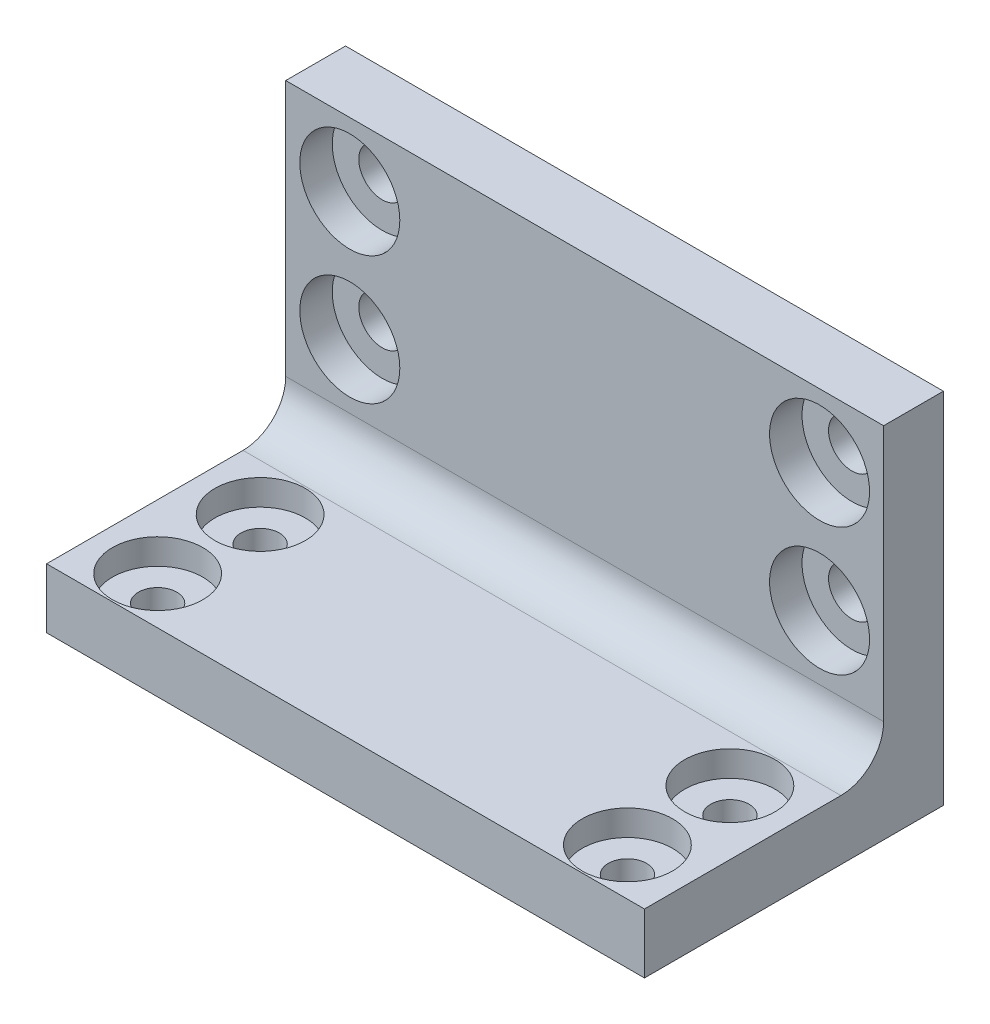
SolidWorks part; units mm, degrees
material "201 Annealed Stainless Steel (SS)"
ref_plane "Front Plane" through (0, 0, 0) normal (0, 0, 1) x (1, 0, 0)
ref_plane "Top Plane" through (0, 0, 0) normal (0, 1, 0) x (1, 0, 0)
ref_plane "Right Plane" through (0, 0, 0) normal (1, 0, 0) x (0, 0, -1)
sketch "Sketch1" plane through (0, 0, 0) normal (0, 1, 0) x (1, 0, 0)
  line L1 (35, -35) -> (-35, -35)
  line L2 (35, -35) -> (35, 0)
  line L3 (35, 0) -> (-35, 0)
  line L4 (-35, -35) -> (-35, 0)
  line L5 (35, -35) -> (-35, 0) construction
  line L6 (35, 0) -> (-35, -35) construction
  point P0 (0, -17.5)
  point P5 (0, 0)
  point P7 (0, 0)
  dimension "D1" = 35
  dimension "D2" = 70
extrude "Boss-Extrude1" add sketch "Sketch1" along normal blind 7
sketch "Sketch2" plane through (0, 7, 0) normal (0, 1, 0) x (1, 0, 0)
  line L1 (35, -7) -> (-35, -7)
  line L2 (35, -7) -> (35, 0)
  line L3 (35, 0) -> (-35, 0)
  line L4 (-35, -7) -> (-35, 0)
  line L5 (35, -7) -> (-35, 0) construction
  line L6 (35, 0) -> (-35, -7) construction
  point P0 (0, -3.5)
  point P6 (0, 0)
  dimension "D1" = 7
extrude "Boss-Extrude2" add sketch "Sketch2" along normal blind 35
fillet "Fillet1" radius 5 1 edges at (0, 7, 7)
sketch "Sketch3" plane through (0, 0, 7) normal (0, 0, 1) x (1, 0, 0)
  line L0 (-35, 42) -> (-35, 12) construction
  line L1 (27.5, 34.5) -> (-27.5, 34.5) construction
  line L2 (27.5, 34.5) -> (27.5, 19.5) construction
  line L3 (27.5, 19.5) -> (-27.5, 19.5) construction
  line L4 (-27.5, 34.5) -> (-27.5, 19.5) construction
  line L5 (27.5, 34.5) -> (-27.5, 19.5) construction
  line L6 (27.5, 19.5) -> (-27.5, 34.5) construction
  point P0 (0, 27)
  point P5 (0, 0)
  point P9 (-35, 27)
  dimension "D1" = 55
  dimension "D2" = 15
hole_wizard "CBORE for M5 Hex Head Machine Screw1" positions "Sketch6" profile "Sketch5" counterbore size "M5" standard "ANSI Metric" end condition through all
sketch "Sketch6" plane through (0, 0, 7) normal (0, 0, 1) x (1, 0, 0)
  point P0 (-27.5, 34.5)
  point P3 (27.5, 34.5)
  point P6 (27.5, 19.5)
  point P9 (-27.5, 19.5)
sketch "Sketch5" plane through (-27.5, 34.5, 7) normal (1, 0, 0) x (0, -1, 0)
  line L0 (0, 0) -> (0, 7)
  line L1 (0, 7) -> (2.75, 7)
  line L3 (2.75, 7) -> (2.75, 3.8)
  line L4 (2.75, 3.8) -> (5.855, 3.8)
  line L5 (5.855, 3.8) -> (5.855, 0)
  line L7 (5.855, 0) -> (0, 0)
  line L11 (0, -6.35) -> (0, 107.95) construction
  dimension "Thru Hole Dia." = 5.5
  dimension "Thru Hole Depth" = 7
  dimension "C'Bore Dia." = 11.71
  dimension "C'Bore Depth" = 3.8
sketch "Sketch7" plane through (0, 7, 0) normal (0, 1, 0) x (1, 0, 0)
  line L0 (-35, -12) -> (-35, -35) construction
  line L1 (27.5, -29.5) -> (-27.5, -29.5)
  line L2 (27.5, -29.5) -> (27.5, -17.5)
  line L3 (27.5, -17.5) -> (-27.5, -17.5)
  line L4 (-27.5, -29.5) -> (-27.5, -17.5)
  line L5 (27.5, -29.5) -> (-27.5, -17.5) construction
  line L6 (27.5, -17.5) -> (-27.5, -29.5) construction
  point P0 (0, -23.5)
  point P5 (0, 0)
  point P8 (-35, -23.5)
  point P9 (0, 0)
  dimension "D1" = 55
  dimension "D2" = 12
hole_wizard "CBORE for M4 Hex Head Machine Screw2" positions "Sketch8" profile "Sketch9" counterbore size "M4" standard "ANSI Metric" end condition through all
sketch "Sketch8" plane through (0, 7, 0) normal (0, 1, 0) x (1, 0, 0)
  point P0 (-27.5, -17.5)
  point P4 (-27.5, -29.5)
  point P7 (27.5, -17.5)
  point P10 (27.5, -29.5)
sketch "Sketch9" plane through (-27.5, 7, 17.5) normal (1, 0, 0) x (0, 0, 1)
  line L0 (0, 0) -> (0, 7)
  line L1 (0, 7) -> (2.25, 7)
  line L3 (2.25, 7) -> (2.25, 3)
  line L4 (2.25, 3) -> (5.295, 3)
  line L5 (5.295, 3) -> (5.295, 0)
  line L7 (5.295, 0) -> (0, 0)
  line L11 (0, -6.35) -> (0, 107.95) construction
  dimension "Thru Hole Dia." = 4.5
  dimension "Thru Hole Depth" = 7
  dimension "C'Bore Dia." = 10.59
  dimension "C'Bore Depth" = 3
